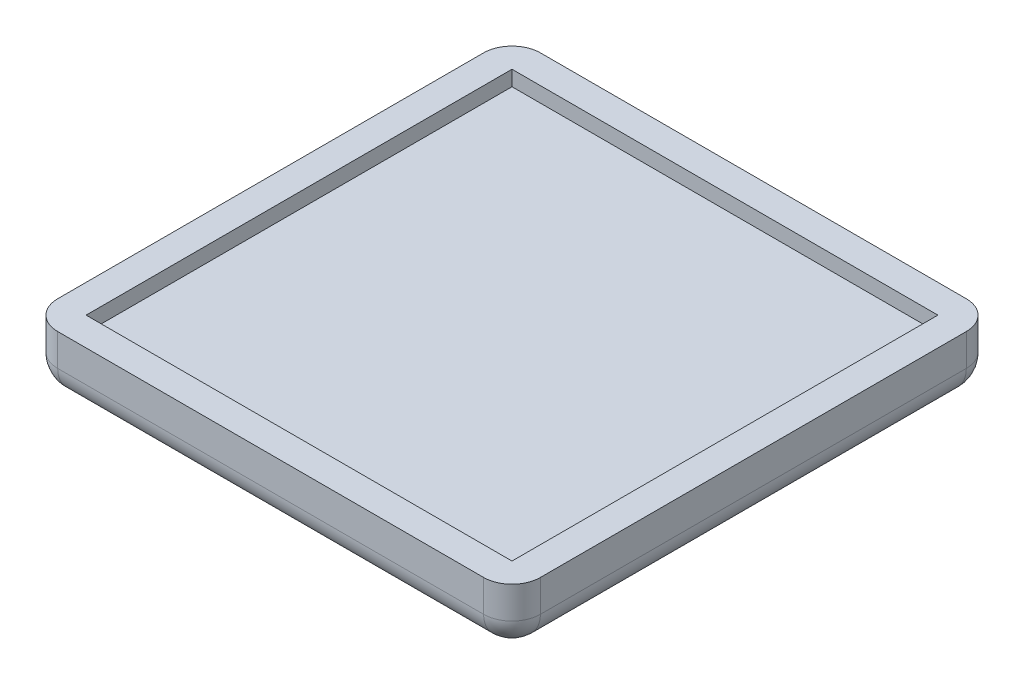
SolidWorks part; units mm, degrees
ref_plane "Front Plane" through (0, 0, 0) normal (0, 0, 1) x (1, 0, 0)
ref_plane "Top Plane" through (0, 0, 0) normal (0, 1, 0) x (1, 0, 0)
ref_plane "Right Plane" through (0, 0, 0) normal (1, 0, 0) x (0, 0, -1)
sketch "Sketch1" plane through (0, 0, 0) normal (0, 1, 0) x (1, 0, 0)
  line L1 (0, 0) -> (76.2, 0)
  line L2 (0, 0) -> (0, 76.2)
  line L3 (0, 76.2) -> (76.2, 76.2)
  line L4 (76.2, 0) -> (76.2, 76.2)
  line L5 (0, 0) -> (-5.08, 0)
  line L6 (0, 0) -> (0, -5.08)
  line L7 (0, -5.08) -> (-5.08, -5.08)
  line L8 (-5.08, 0) -> (-5.08, -5.08)
  line L9 (76.2, 76.2) -> (81.28, 76.2)
  line L10 (76.2, 76.2) -> (76.2, 81.28)
  line L11 (76.2, 81.28) -> (81.28, 81.28)
  line L12 (81.28, 76.2) -> (81.28, 81.28)
  line L13 (-5.08, -5.08) -> (81.28, -5.08)
  line L14 (-5.08, -5.08) -> (-5.08, 81.28)
  line L15 (-5.08, 81.28) -> (81.28, 81.28)
  line L16 (81.28, -5.08) -> (81.28, 81.28)
  dimension "D1" = 76.2
  dimension "D2" = 76.2
  dimension "D3" = 5.08
  dimension "D4" = 5.08
  dimension "D5" = 5.08
  dimension "D6" = 5.08
extrude "Boss-Extrude1" add sketch "Sketch1" against normal blind 5.715 contours L15 L14 L5 L2 L3 L10 | L13 L16 L9 L4 L1 L6 | L5 L8 L7 L6 | L9 L12 L11 L10
sketch "Sketch2" plane through (0, -5.715, 0) normal (0, -1, 0) x (-1, 0, 0)
  line L1 (5.08, 81.28) -> (-81.28, 81.28)
  line L2 (5.08, 81.28) -> (5.08, -5.08)
  line L3 (5.08, -5.08) -> (-81.28, -5.08)
  line L4 (-81.28, 81.28) -> (-81.28, -5.08)
extrude "Boss-Extrude2" add sketch "Sketch2" along normal blind 5.08
fillet "Fillet1" radius 5.08 8 edges at (-5.08, -5.3975, 5.08) (38.1, -10.795, 5.08) (81.28, -5.3975, 5.08) (81.28, -10.795, -38.1) (81.28, -5.3975, -81.28) (38.1, -10.795, -81.28) (-5.08, -5.3975, -81.28) (-5.08, -10.795, -38.1)
sketch "Sketch3" plane through (0, -5.715, 0) normal (0, 1, 0) x (1, 0, 0)
  line L1 (76.2, 76.2) -> (0, 76.2)
  line L2 (76.2, 76.2) -> (76.2, 0)
  line L3 (76.2, 0) -> (0, 0)
  line L4 (0, 76.2) -> (0, 0)
extrude "Boss-Extrude3" add sketch "Sketch3" along normal blind 3
sketch "Sketch4" plane through (0, -2.715, 0) normal (0, 1, 0) x (1, 0, 0)
  line L0 (76.2, 76.2) -> (0, 0)
  line L1 (0, 76.2) -> (76.2, 0)
  line L3 (12.7, 2.921) -> (63.5, 2.921)
  line L4 (12.7, 2.921) -> (12.7, 73.279)
  line L5 (12.7, 73.279) -> (63.5, 73.279)
  line L6 (63.5, 2.921) -> (63.5, 73.279)
  line L7 (12.7, 2.921) -> (63.5, 73.279) construction
  line L8 (12.7, 73.279) -> (63.5, 2.921) construction
  line L13 (24.0473, -0.9354) -> (49.53, 69.85) construction
  line L14 (3.81, 69.85) -> (60.0821, 17.7462) construction
  point P8 (38.1, 38.1)
  point P13 (38.1, 38.1)
